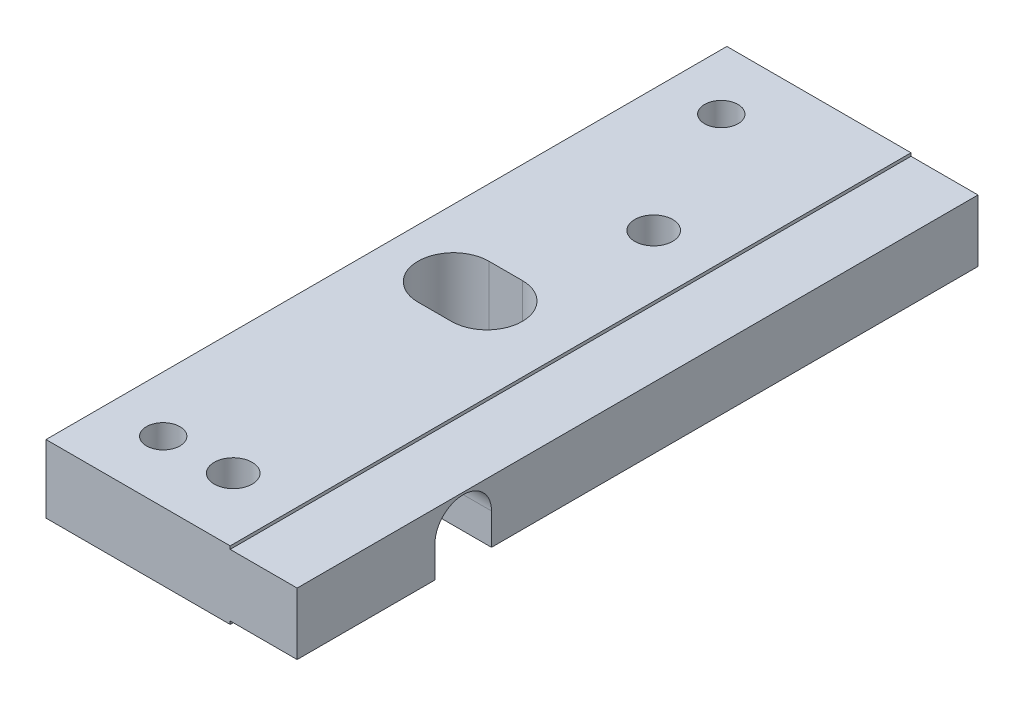
SolidWorks part; units mm, degrees
material "Generic Carbon Fiber"
ref_plane "Front Plane" through (0, 0, 0) normal (0, 0, 1) x (1, 0, 0)
ref_plane "Top Plane" through (0, 0, 0) normal (0, 1, 0) x (1, 0, 0)
ref_plane "Right Plane" through (0, 0, 0) normal (1, 0, 0) x (0, 0, -1)
sketch "Sketch1" plane through (0, 0, 0) normal (1, 0, 0) x (0, 0, -1)
  line L1 (0, -3.05) -> (61, -3.05)
  line L2 (0, -3.05) -> (0, 3.05)
  line L3 (0, 3.05) -> (61, 3.05)
  line L4 (61, -3.05) -> (61, 3.05)
  dimension "D1" = 61
  dimension "D2" = 6.1
extrude "Boss-Extrude1" add sketch "Sketch1" along normal blind 22.5
sketch "Sketch2" plane through (22.5, 0, 0) normal (1, 0, 0) x (0, 0, -1)
  line L0 (0, 3.05) -> (0, -3.05) construction
  line L1 (0, -2.775) -> (61, -2.775)
  line L2 (0, -2.775) -> (0, 2.775)
  line L3 (0, 2.775) -> (61, 2.775)
  line L4 (61, -2.775) -> (61, 2.775)
  line L5 (61, -3.05) -> (61, 3.05) construction
  line L7 (30.5, 3.05) -> (30.5, -3.05) construction
  line L8 (61, 3.05) -> (0, 3.05) construction
  line L9 (0, -3.05) -> (61, -3.05) construction
  line L10 (0, 0) -> (30.5, 0) construction
  dimension "D1" = 5.55
extrude "Cut-Extrude1" cut sketch "Sketch2" against normal blind 6 flip side to cut
sketch "Sketch5" plane through (0, 0, 0) normal (-1, 0, 0) x (0, 0, 1)
  line L0 (-14.881, 0.0496) -> (0, 0.0496) construction
  line L1 (-61, 2.775) -> (0, 2.775) construction
  line L2 (0, 3.05) -> (0, -3.05) construction
  line L3 (0, -3.05) -> (-61, -3.05) construction
  line L4 (-12.3486, 0.0496) -> (-12.3486, -3.05)
  line L5 (-12.3486, -3.05) -> (-17.4134, -3.05)
  line L6 (-17.4134, -3.05) -> (-17.4134, 0.0496)
  arc A0 (-12.3486, 0.0496) -> (-17.4134, 0.0496) centre (-14.881, 0.0496) ccw
  dimension "D1" = 5.0648
  dimension "D2" = 14.881
  dimension "D3" = 2.7254
extrude "Cut-Extrude3" cut sketch "Sketch5" against normal through all
sketch "Sketch6" plane through (0, 3.05, 0) normal (0, 1, 0) x (1, 0, 0)
  line L0 (0, 30.5) -> (22.5, 30.5) construction
  line L1 (9, 30.5) -> (6, 30.5) construction
  line L2 (22.5, 61) -> (22.5, 0) construction
  line L4 (0, 61) -> (0, 0) construction
  line L5 (9, 27.325) -> (6, 27.325)
  line L6 (9, 33.675) -> (6, 33.675)
  arc A0 (9, 27.325) -> (9, 33.675) centre (9, 30.5) ccw
  arc A1 (6, 33.675) -> (6, 27.325) centre (6, 30.5) ccw
  point P7 (7.5, 30.5)
  dimension "D2" = 3.175
  dimension "D1" = 3
  dimension "D3" = 6
extrude "Cut-Extrude4" cut sketch "Sketch6" against normal through all
sketch "Sketch7" plane through (0, 3.05, 0) normal (0, 1, 0) x (1, 0, 0)
  line L0 (5, 61) -> (5, 0) construction
  line L1 (16.5, 61) -> (0, 61) construction
  line L2 (16.5, 0) -> (0, 0) construction
  line L3 (0, 30.5) -> (22.5, 30.5) construction
  line L4 (0, 61) -> (0, 0) construction
  line L5 (22.5, 61) -> (22.5, 0) construction
  circle A0 centre (5, 55.5) radius 1.5
  circle A1 centre (5, 5.5) radius 1.5
  dimension "D1" = 3
  dimension "D2" = 5
  dimension "D3" = 25
  dimension "D4" = 25
extrude "Cut-Extrude5" cut sketch "Sketch7" against normal through all
hole_wizard "CBORE for M3 Pan Head Machine Screw2" positions "Sketch14" profile "Sketch13" counterbore size "M3" standard "ANSI Metric" end condition through all
sketch "Sketch14" plane through (0, -3.05, 0) normal (0, -1, 0) x (-1, 0, 0)
  line L1 (-16.5, 0) -> (0, 0) construction
  point P0 (-11, 5.772)
  point P2 (-11, 43.447)
  dimension "D1" = 37.675
  dimension "D2" = 5.772
sketch "Sketch13" plane through (11, -3.05, -5.772) normal (1, 0, 0) x (0, 0, -1)
  line L0 (0, 0) -> (0, 6.1)
  line L1 (0, 6.1) -> (1.7, 6.1)
  line L3 (1.7, 6.1) -> (1.7, 2.2)
  line L4 (1.7, 2.2) -> (3.25, 2.2)
  line L5 (3.25, 2.2) -> (3.25, 0)
  line L7 (3.25, 0) -> (0, 0)
  line L11 (0, -6.35) -> (0, 107.95) construction
  dimension "Thru Hole Dia." = 3.4
  dimension "Thru Hole Depth" = 6.1
  dimension "C'Bore Dia." = 6.5
  dimension "C'Bore Depth" = 2.2
